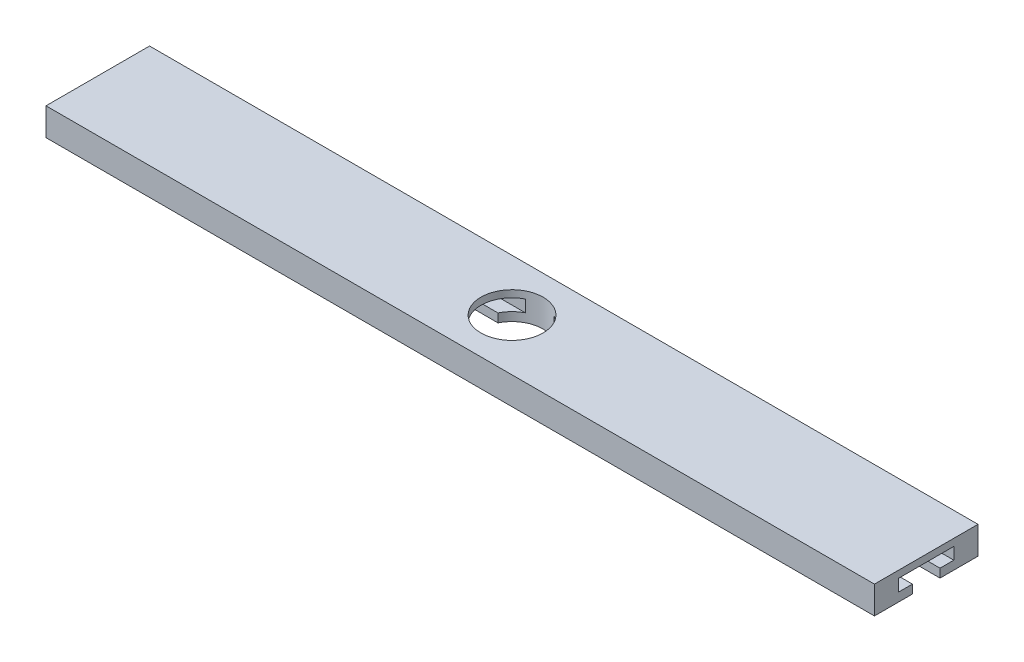
SolidWorks part; units mm, degrees
ref_plane "Front Plane" through (0, 0, 0) normal (0, 0, 1) x (1, 0, 0)
ref_plane "Top Plane" through (0, 0, 0) normal (0, 1, 0) x (1, 0, 0)
ref_plane "Right Plane" through (0, 0, 0) normal (1, 0, 0) x (0, 0, -1)
sketch "Sketch1" plane through (0, 0, 0) normal (0, 0, 1) x (1, 0, 0)
  line L3 (-99.2685, 34.4475) -> (20.7315, 34.4475)
  line L4 (-99.2685, 30.4475) -> (20.7315, 30.4475)
  line L5 (20.7315, 30.4475) -> (20.7315, 34.4475)
  line L6 (-99.2685, 34.4475) -> (-99.2685, 30.4475)
extrude "Boss-Extrude1" add sketch "Sketch1" along normal blind 15
sketch "Sketch2" plane through (0, 0, 0) normal (1, 0, 0) x (0, 0, -1)
sketch "Sketch3" plane through (0, 0, 0) normal (1, 0, 0) x (0, 0, -1)
  line L0 (-9.5, 30.4475) -> (-5.5, 30.4475)
  line L4 (-15, 30.4475) -> (0, 30.4475) construction
  line L11 (-11.5, 33.4296) -> (-3.5, 33.4296)
  line L12 (-3.5, 33.4296) -> (-3.5, 31.6992)
  line L13 (-3.5, 31.6992) -> (-5.5, 31.6992)
  line L14 (-5.5, 31.6992) -> (-5.5, 30.4475)
  line L16 (-9.5, 30.4475) -> (-9.5, 31.6992)
  line L17 (-9.5, 31.6992) -> (-11.5, 31.6992)
  line L18 (-11.5, 31.6992) -> (-11.5, 33.4296)
extrude "Cut-Extrude1" cut sketch "Sketch3" against normal blind 130 and the other way blind 27
sketch "Sketch4" plane through (0, 0, 0) normal (0, 1, 0) x (1, 0, 0)
  circle A0 centre (-39.2685, -7.5) radius 4.5
extrude "Cut-Extrude2" cut sketch "Sketch4" along normal blind 44
